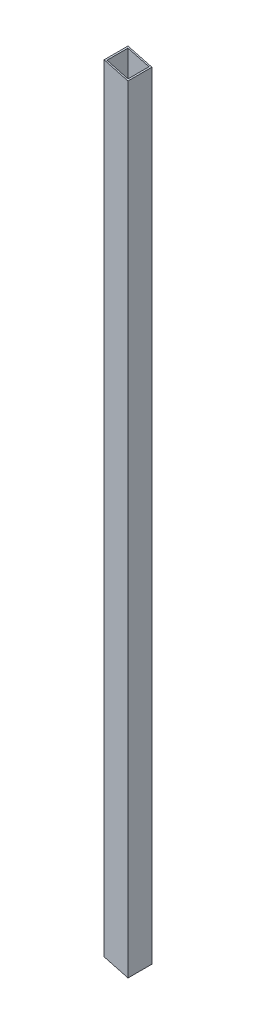
SolidWorks part; units mm, degrees
ref_plane "Front Plane" through (0, 0, 0) normal (0, 0, 1) x (1, 0, 0)
ref_plane "Top Plane" through (0, 0, 0) normal (0, 1, 0) x (1, 0, 0)
ref_plane "Right Plane" through (0, 0, 0) normal (1, 0, 0) x (0, 0, -1)
sketch "Sketch1" plane through (0, 0, 0) normal (0, 1, 0) x (1, 0, 0)
  line L1 (-25.4, 17.3952) -> (0, 17.3952)
  line L2 (-25.4, 17.3952) -> (-25.4, -8.0048)
  line L3 (-25.4, -8.0048) -> (0, -8.0048)
  line L4 (0, 17.3952) -> (0, -8.0048)
  line L5 (-23.876, 15.8712) -> (-1.524, 15.8712)
  line L6 (-23.876, 15.8712) -> (-23.876, -6.4808)
  line L7 (-23.876, -6.4808) -> (-1.524, -6.4808)
  line L8 (-1.524, 15.8712) -> (-1.524, -6.4808)
  dimension "D1" = 25.4
  dimension "D2" = 25.4
  dimension "D3" = 1.524
  dimension "D4" = 1.524
  dimension "D5" = 1.524
  dimension "D6" = 1.524
extrude "Boss-Extrude1" add sketch "Sketch1" along normal blind 877.062
sketch "Sketch2" plane through (0, 0, 8.0048) normal (0, 0, 1) x (1, 0, 0)
  line L0 (-25.4, 877.062) -> (0, 870.2561)
  line L2 (0, 877.062) -> (0, 0) construction
  line L3 (0, 870.2561) -> (0, 877.062)
  line L4 (0, 877.062) -> (-25.4, 877.062)
  dimension "D1" = 15
extrude "Cut-Extrude1" cut sketch "Sketch2" against normal through all both and the other way through all
sketch "Sketch3" plane through (0, 0, -17.3952) normal (0, 0, -1) x (-1, 0, 0)
  line L0 (25.4, 0) -> (25.4, 50.8)
  line L1 (25.4, 877.062) -> (25.4, 0) construction
  line L2 (25.4, 50.8) -> (0, 43.9941)
  line L3 (0, 870.2561) -> (0, 0) construction
  line L4 (0, 43.9941) -> (0, 0)
  line L5 (0, 0) -> (25.4, 0)
  dimension "D1" = 50.8
  dimension "D2" = 75
extrude "Cut-Extrude2" cut sketch "Sketch3" against normal through all both and the other way through all
